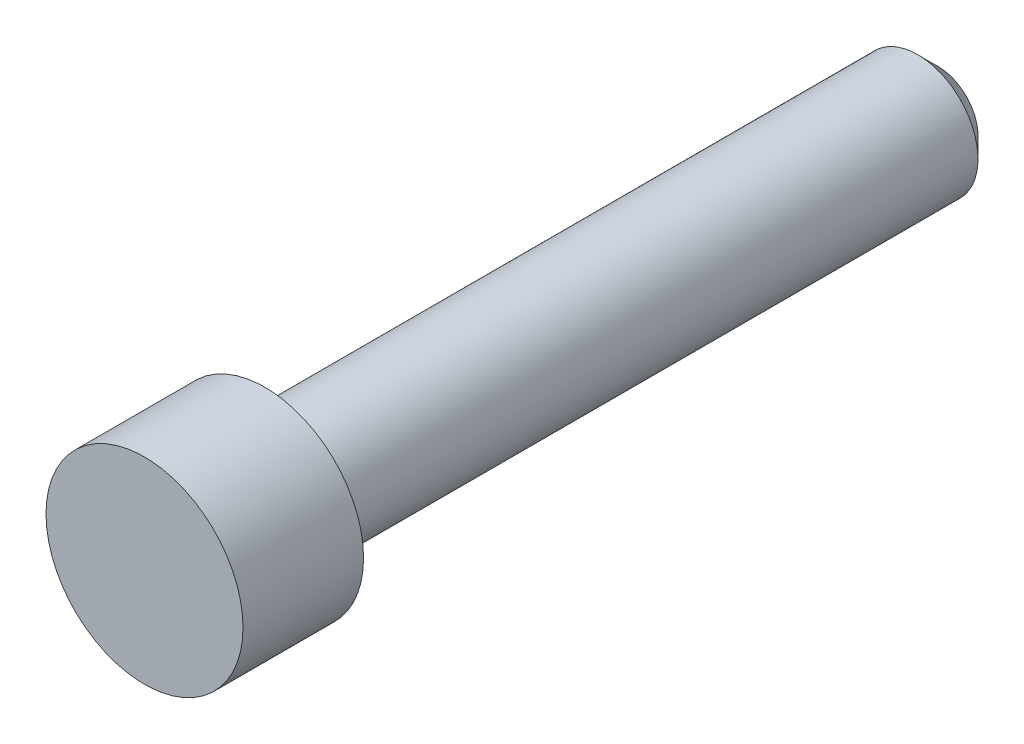
SolidWorks part; units mm, degrees
ref_plane "Front Plane" through (0, 0, 0) normal (0, 0, 1) x (1, 0, 0)
ref_plane "Top Plane" through (0, 0, 0) normal (0, 1, 0) x (1, 0, 0)
ref_plane "Right Plane" through (0, 0, 0) normal (1, 0, 0) x (0, 0, -1)
sketch "Sketch1" plane through (0, 0, 0) normal (1, 0, 0) x (0, 0, -1)
  line L0 (9.3599, 0) -> (-9.3599, 0) construction
  line L1 (-9.3599, 0) -> (-9.3599, 2.3241) construction
  line L2 (-6.5151, 1.4224) -> (-6.5151, 0) construction
  line L3 (8.7249, 0) -> (8.7249, 0.635) construction
  line L4 (-6.5151, 0) -> (-6.5151, -1.4224) construction
  line L5 (9.3599, 1.4224) -> (9.3599, -1.4224) construction
  line L6 (-6.5151, 1.4224) -> (-6.5151, 2.3241) construction
  point P6 (-9.3599, 1.1906)
  point P9 (-9.3599, -1.1906)
  point P10 (-6.5151, 0)
  point P13 (7.1374, -1.4224)
  dimension "Head Diameter" = 4.6482
  dimension "Head Height" = 2.8448
  dimension "Screw Size Decimal Equivalent" = 2.8448
  dimension "Length" = 15.875
  dimension "Pitch" = 0.635
  dimension "Drive Size" = 2.3813
  dimension "D1" = 0.635
  dimension "D2" = 2.2225
sketch "Sketch2" plane through (0, 0, 0) normal (1, 0, 0) x (0, 0, -1)
  line L0 (9.3599, 0.9461) -> (8.8836, 1.4224)
  line L1 (-9.3599, 2.3241) -> (-6.5151, 2.3241)
  line L2 (-9.3599, 2.3241) -> (-9.3599, 0)
  line L4 (-6.5151, 2.3241) -> (-6.5151, 1.4224)
  line L5 (-6.5151, 1.4224) -> (8.8836, 1.4224)
  line L8 (9.3599, 0.9461) -> (9.3599, 0)
  line L9 (9.3599, 0) -> (-9.3599, 0) construction
  line L10 (9.3599, 0) -> (-9.3599, 0)
  dimension "D1" = 135
  dimension "D2" = 0.4763
revolve "Revolve1" add sketch "Sketch2" angle 360 about L10
equation "\"Pitch Natural Taper Angle\"= ATN ( \"Pitch@Sketch1\" / 2 )"
equation "\"Rounded Angle Count\"= ROUND ( 60 / \"Pitch Natural Taper Angle\" )"
equation "\"Taper Angle\"= \"Rounded Angle Count\" * \"Pitch Natural Taper Angle\""
equation "\"D1@Sketch1\"=\"Pitch@Sketch1\""
equation "\"D2@Sketch2\"=\"D1@Sketch1\"*.75"
equation "\"D2@Sketch1\"=\"Pitch@Sketch1\"*3.5"
